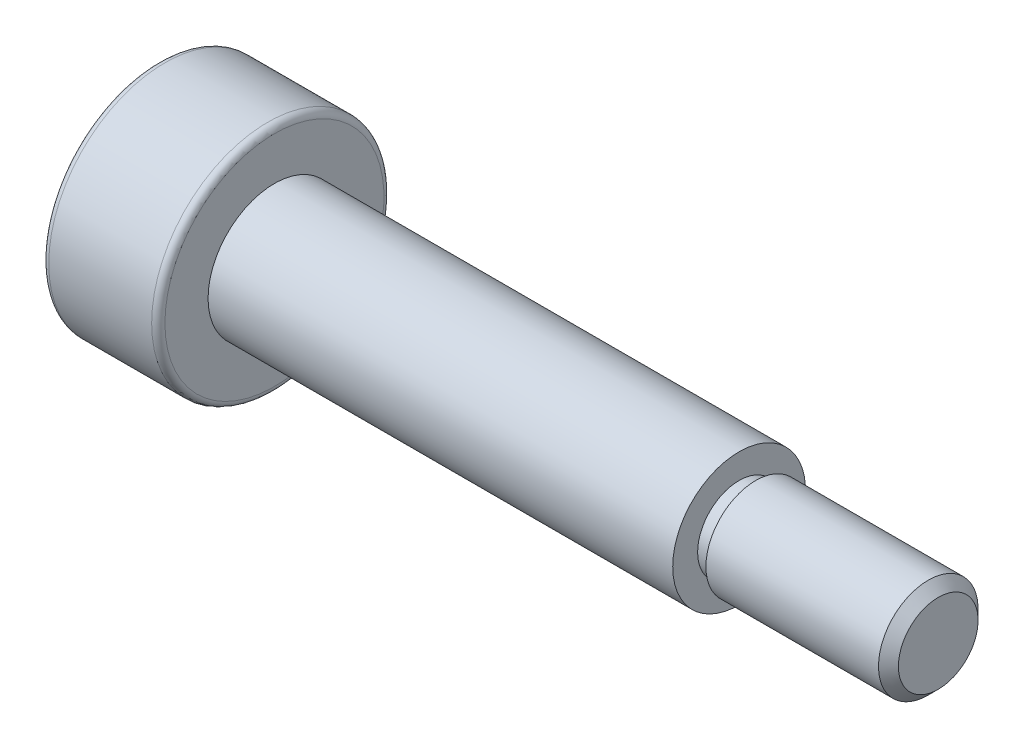
SolidWorks part; units mm, degrees
ref_plane "前视基准面" through (0, 0, 0) normal (0, 0, 1) x (1, 0, 0)
ref_plane "上视基准面" through (0, 0, 0) normal (0, 1, 0) x (1, 0, 0)
ref_plane "右视基准面" through (0, 0, 0) normal (1, 0, 0) x (0, 0, -1)
sketch "草图1" plane through (0, 0, 0) normal (0, 0, 1) x (1, 0, 0)
  line L0 (-11.75, 0) -> (11.75, 0) construction
  line L1 (-11.75, 0) -> (-11.75, 3.5)
  line L2 (-11.75, 3.5) -> (-8.25, 3.5)
  line L3 (-8.25, 3.5) -> (-8.25, 2)
  line L4 (-8.25, 2) -> (5.75, 2)
  line L5 (5.75, 2) -> (5.75, 1.5)
  line L6 (5.75, 1.5) -> (11.75, 1.5)
  line L7 (11.75, 1.5) -> (11.75, 0)
  line L8 (-11.75, 0) -> (11.75, 0)
  dimension "D1" = 4
  dimension "D2" = 7
  dimension "D3" = 3
  dimension "D4" = 6
  dimension "D5" = 14
  dimension "D6" = 3.5
revolve "旋转1" add sketch "草图1" angle 360 about L0
fillet "圆角1" radius 0.2 2 edges at (-8.25, 0, 3.5) (-11.75, 0, 3.5)
chamfer "倒角1" distance 0.3 angle 45 1 edges at (11.75, 0, 1.5)
sketch "草图3" plane through (0, 0, 0) normal (0, 0, 1) x (1, 0, 0)
  line L0 (5.75, 0) -> (11.45, 0) construction
  line L1 (5.75, -1.5) -> (5.75, 1.5) construction
  line L2 (11.45, 1.5) -> (11.45, -1.5) construction
  line L3 (5.75, -2) -> (5.75, 2) construction
  line L4 (5.75, 1.5) -> (6.25, 1.5)
  line L5 (5.75, 1.5) -> (5.75, 1.25)
  line L6 (5.75, 1.25) -> (6.25, 1.25)
  line L7 (6.25, 1.5) -> (6.25, 1.25)
  line L8 (11.45, 1.5) -> (5.75, 1.5) construction
  dimension "D1" = 2.5
  dimension "D2" = 0.5
revolve "切除-旋转1" cut sketch "草图3" angle 360 about L0
sketch "草图4" plane through (-11.75, 0, 0) normal (-1, 0, 0) x (0, 0, 1)
  line L1 (1.7321, 0) -> (0.866, 1.5)
  line L2 (0.866, 1.5) -> (-0.866, 1.5)
  line L3 (-0.866, 1.5) -> (-1.7321, 0)
  line L4 (-1.7321, 0) -> (-0.866, -1.5)
  line L5 (-0.866, -1.5) -> (0.866, -1.5)
  line L6 (0.866, -1.5) -> (1.7321, 0)
  circle A0 centre (0, 0) radius 1.5 construction
  dimension "D1" = 3
extrude "切除-拉伸1" cut sketch "草图4" against normal blind 2
